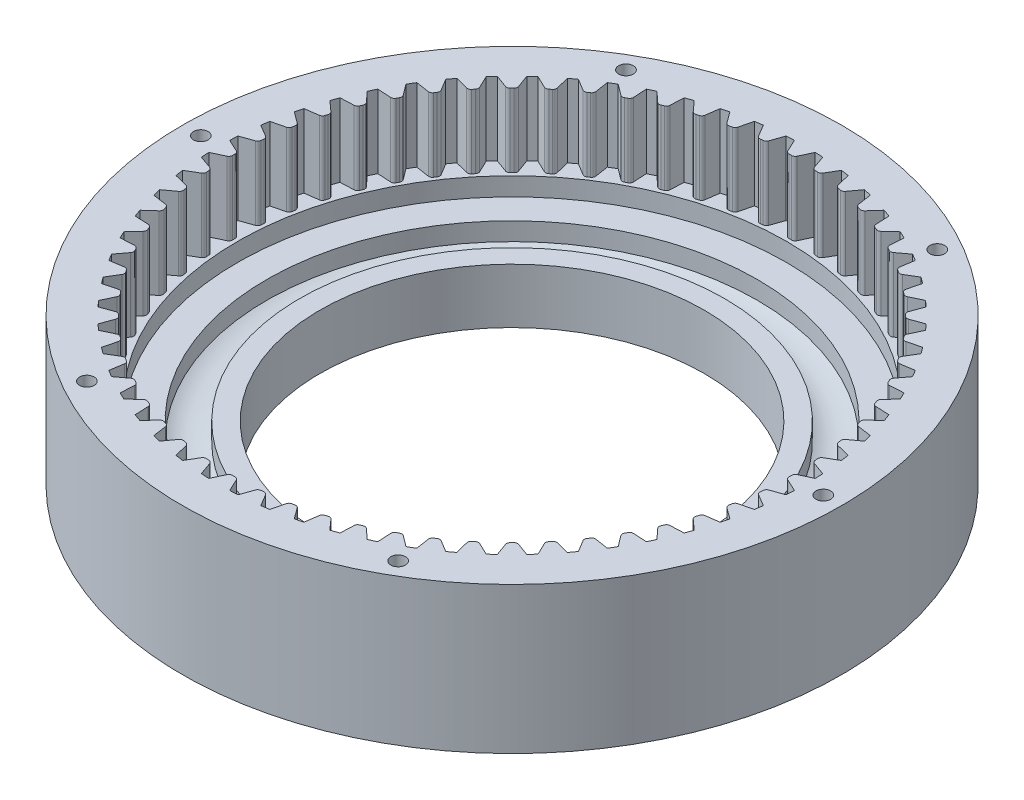
SolidWorks part; units mm, degrees
ref_plane "Front Plane" through (0, 0, 0) normal (0, 0, 1) x (1, 0, 0)
ref_plane "Top Plane" through (0, 0, 0) normal (0, 1, 0) x (1, 0, 0)
ref_plane "Right Plane" through (0, 0, 0) normal (1, 0, 0) x (0, 0, -1)
sketch "Sketch1" plane through (0, 0, 0) normal (0, 0, 1) x (1, 0, 0)
  line L0 (0, 0) -> (0, 36.773) construction
  line L2 (-90, 0) -> (-90, 40)
  line L3 (-90, 40) -> (-80, 40)
  line L4 (-80, 40) -> (-80, 20)
  line L5 (-75, 15) -> (-67, 15)
  line L6 (-67, 15) -> (-67, 10.0697)
  line L7 (-58, 10.0697) -> (-58, 15)
  line L8 (-58, 15) -> (-52.5, 15)
  line L10 (-67, 15) -> (-58, 15) construction
  line L12 (-52.5, 15) -> (-52.5, 0)
  line L16 (-52.5, 0) -> (-90, 0)
  line L18 (-80, 20) -> (-75, 20)
  line L19 (-75, 20) -> (-75, 15)
  arc A0 (-67, 10.0697) -> (-58, 10.0697) centre (-62.5, 19) ccw
  point P14 (-62.5, 15)
  point P16 (-62.5, 9)
  dimension "D5" = 10
  dimension "D2" = 150
  dimension "D3" = 40
  dimension "D4" = 9
  dimension "D6" = 6
  dimension "D7" = 160
  dimension "D8" = 15
  dimension "D9" = 105
  dimension "D12" = 20
  dimension "D13" = 180
  dimension "D14" = 125
revolve "Revolve1" add sketch "Sketch1" angle 360 about L0
sketch "Sketch2" plane through (0, 20, 0) normal (0, 1, 0) x (1, 0, 0)
  line L0 (-79.9495, 2.8417) -> (-76.5774, 1.2692)
  line L1 (-76.5774, -1.2692) -> (-79.9495, -2.8417)
  line L2 (-76, -0.3629) -> (-76, 0.3629)
  circle A1 centre (0, 0) radius 80 construction
  circle A2 centre (0, 0) radius 80 construction
  arc A4 (-79.9495, 2.8417) -> (-79.9495, -2.8417) centre (0, 0) ccw
  arc A5 (-76, -0.3629) -> (-76.5774, -1.2692) centre (-77, -0.3629) cw
  arc A6 (-76.5774, 1.2692) -> (-76, 0.3629) centre (-77, 0.3629) cw
  point P9 (-76, -1)
  point P11 (-80, 0)
  point P15 (-76, 1)
  dimension "D1" = 4
  dimension "D4" = 1
  dimension "D2" = 50
  dimension "D3" = 2
extrude "Boss-Extrude1" add sketch "Sketch2" along normal up to surface (20 mm away) up to face at (0, 40, -90)
pattern_circular "CirPattern1" count 64 over 360 about axis through (0, 0, 0) along (0, 1, 0) of "Boss-Extrude1"
sketch "Sketch3" plane through (0, 40, 0) normal (0, 1, 0) x (1, 0, 0)
  circle A0 centre (-85, 0) radius 2
  dimension "D2" = 4
  dimension "D1" = 85
extrude "Cut-Extrude1" cut sketch "Sketch3" against normal blind 15
pattern_circular "CirPattern2" count 6 over 360 about axis through (0, 0, 0) along (0, 1, 0) of "Cut-Extrude1"
sketch "Sketch4" plane through (0, 0, 0) normal (0, -1, 0) x (-1, 0, 0)
  circle A0 centre (78, 0) radius 4
  dimension "D1" = 8
  dimension "D2" = 78
extrude "Cut-Extrude2" cut sketch "Sketch4" against normal blind 12
pattern_circular "CirPattern3" count 4 over 360 about axis through (0, 0, 0) along (0, 1, 0) of "Cut-Extrude2"
